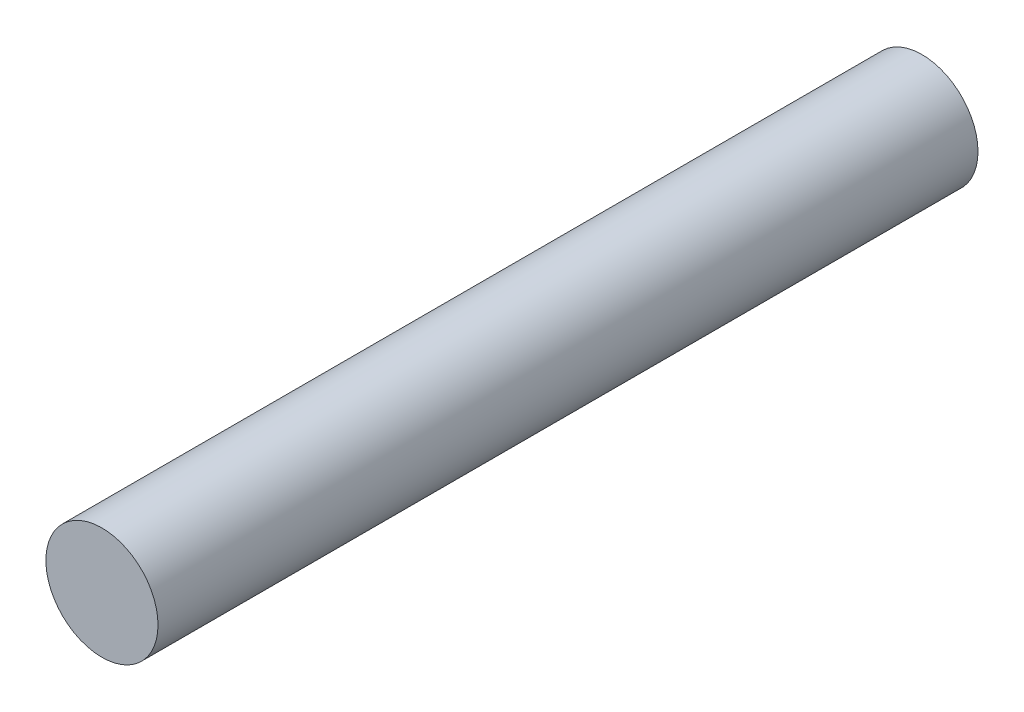
SolidWorks part; units mm, degrees
material "Plain Carbon Steel"
ref_plane "Front Plane" through (0, 0, 0) normal (0, 0, 1) x (1, 0, 0)
ref_plane "Top Plane" through (0, 0, 0) normal (0, 1, 0) x (1, 0, 0)
ref_plane "Right Plane" through (0, 0, 0) normal (1, 0, 0) x (0, 0, -1)
sketch "Sketch1" plane through (0, 0, 0) normal (0, 0, 1) x (1, 0, 0)
  circle A0 centre (0, 0) radius 2.3876
  dimension "D1" = 4.7752
extrude "Boss-Extrude1" add sketch "Sketch1" along normal mid plane 34.925
